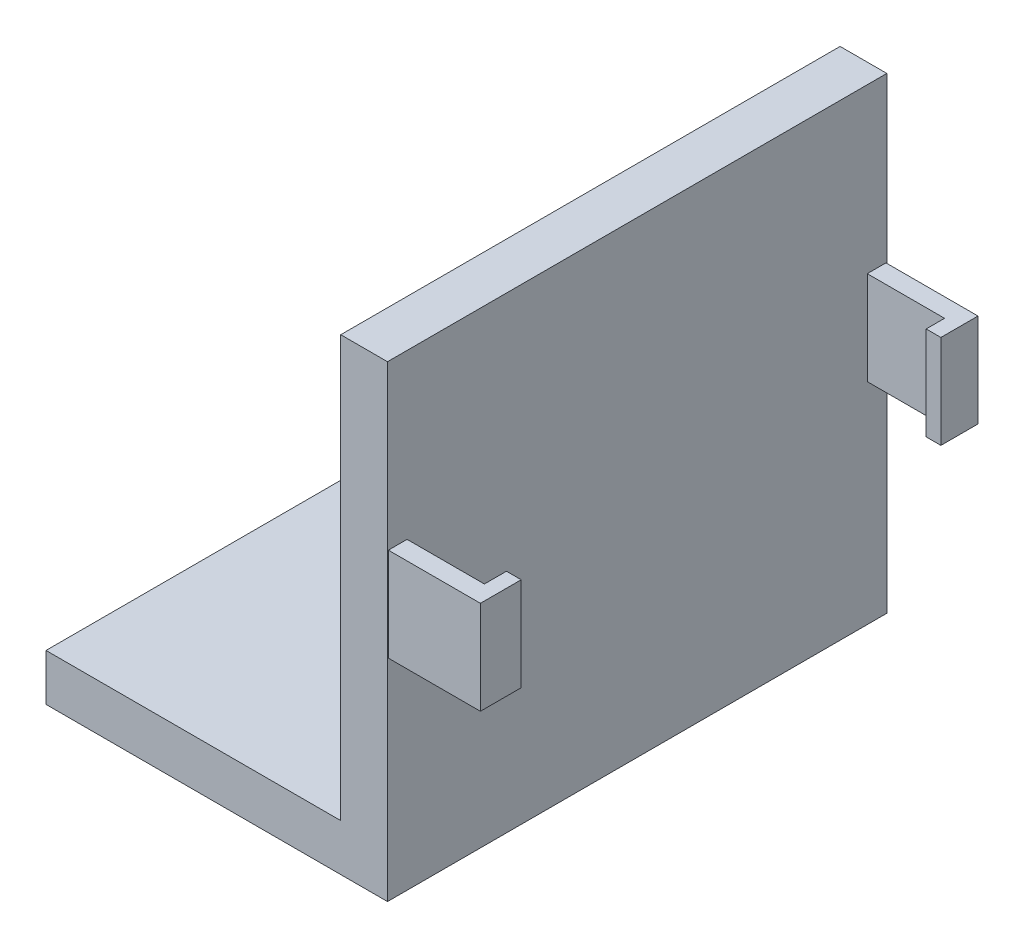
SolidWorks part; units mm, degrees
ref_plane "Front Plane" through (0, 0, 0) normal (0, 0, 1) x (1, 0, 0)
ref_plane "Top Plane" through (0, 0, 0) normal (0, 1, 0) x (1, 0, 0)
ref_plane "Right Plane" through (0, 0, 0) normal (1, 0, 0) x (0, 0, -1)
sketch "Sketch1" plane through (0, 0, 0) normal (0, 1, 0) x (1, 0, 0)
  circle A0 centre (0, 0) radius 50.8
extrude "Boss-Extrude1" add sketch "Sketch1" along normal blind 6.35
sketch "Sketch2" plane through (0, 6.35, 0) normal (0, 1, 0) x (1, 0, 0)
  line L1 (14.6299, 33.909) -> (20.9799, 33.909)
  line L2 (14.6299, 33.909) -> (14.6299, -33.909)
  line L3 (14.6299, -33.909) -> (20.9799, -33.909)
  line L4 (20.9799, 33.909) -> (20.9799, -33.909)
  dimension "D1" = 33.909
  dimension "D2" = 33.909
  dimension "D3" = 6.35
extrude "Boss-Extrude2" add sketch "Sketch2" along normal blind 57.15
sketch "Sketch3" plane through (20.9799, 0, 0) normal (1, 0, 0) x (0, 0, -1)
  line L0 (0, 63.5) -> (0, 6.35) construction
  line L1 (-33.909, 63.5) -> (33.909, 63.5) construction
  line L2 (-33.909, 6.35) -> (33.909, 6.35) construction
  line L3 (-31.25, 28.575) -> (-33.79, 28.575)
  line L4 (31.25, 41.275) -> (33.79, 41.275)
  line L5 (31.25, 41.275) -> (31.25, 28.575)
  line L6 (31.25, 28.575) -> (33.79, 28.575)
  line L7 (33.79, 41.275) -> (33.79, 28.575)
  line L8 (-33.79, 41.275) -> (-33.79, 28.575)
  line L9 (-31.25, 41.275) -> (-33.79, 41.275)
  line L10 (-31.25, 41.275) -> (-31.25, 28.575)
  dimension "D1" = 2.54
  dimension "D2" = 12.7
  dimension "D3" = 22.225
  dimension "D4" = 31.25
extrude "Boss-Extrude3" add sketch "Sketch3" along normal blind 12.5
sketch "Sketch4" plane through (0, 0, 31.25) normal (0, 0, -1) x (-1, 0, 0)
  line L0 (-33.4799, 28.575) -> (-20.9799, 28.575) construction
  line L1 (-33.4799, 41.275) -> (-31.4799, 41.275)
  line L2 (-33.4799, 41.275) -> (-33.4799, 28.575)
  line L3 (-33.4799, 28.575) -> (-31.4799, 28.575)
  line L4 (-31.4799, 41.275) -> (-31.4799, 28.575)
  dimension "D1" = 2
extrude "Boss-Extrude4" add sketch "Sketch4" along normal blind 3
sketch "Sketch5" plane through (0, 0, -31.25) normal (0, 0, 1) x (1, 0, 0)
  line L0 (33.4799, 28.575) -> (20.9799, 28.575) construction
  line L1 (33.4799, 41.275) -> (31.4799, 41.275)
  line L2 (33.4799, 41.275) -> (33.4799, 28.575)
  line L3 (33.4799, 28.575) -> (31.4799, 28.575)
  line L4 (31.4799, 41.275) -> (31.4799, 28.575)
  dimension "D1" = 2
extrude "Boss-Extrude5" add sketch "Sketch5" along normal blind 2.5
sketch "Sketch6" plane through (0, 6.35, 0) normal (0, 1, 0) x (1, 0, 0)
  line L0 (14.6299, -33.909) -> (20.9799, -33.909) construction
  line L1 (20.9799, 33.909) -> (-25.4, 33.909)
  line L2 (20.9799, 33.909) -> (20.9799, -33.909)
  line L3 (20.9799, -33.909) -> (-25.4, -33.909)
  line L4 (-25.4, 33.909) -> (-25.4, -33.909)
  dimension "D1" = 0
  dimension "D2" = 25.4
extrude "Cut-Extrude1" cut sketch "Sketch6" against normal through all flip side to cut
